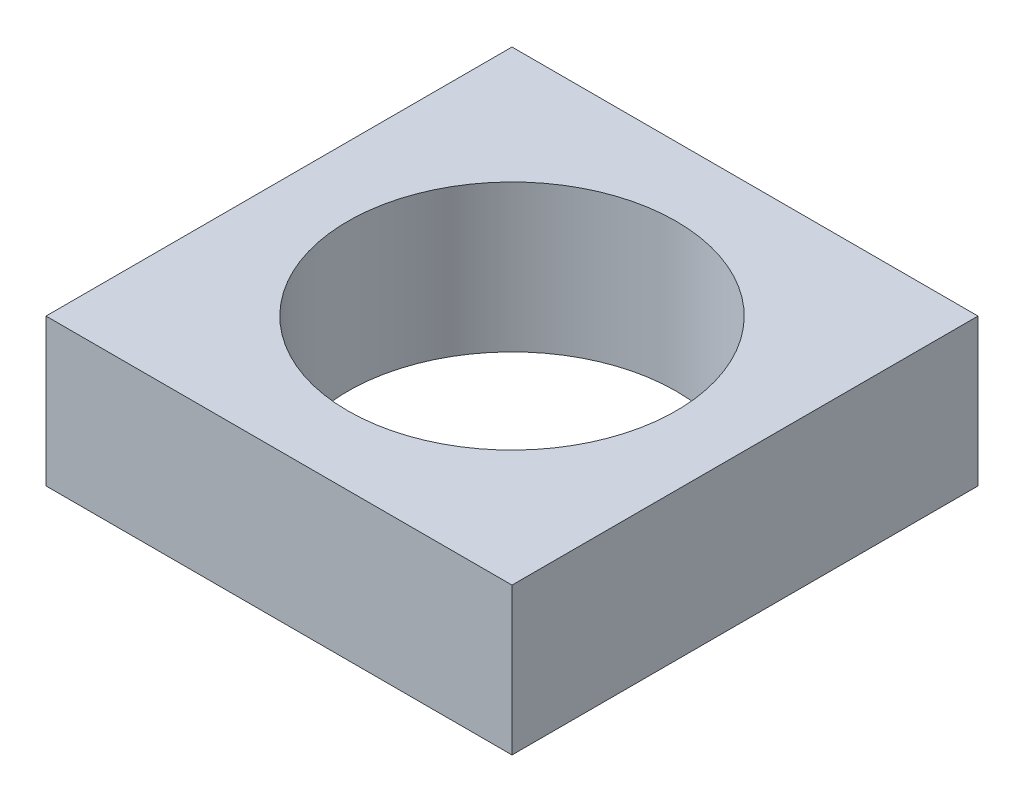
SolidWorks part; units mm, degrees
ref_plane "Front Plane" through (0, 0, 0) normal (0, 0, 1) x (1, 0, 0)
ref_plane "Top Plane" through (0, 0, 0) normal (0, 1, 0) x (1, 0, 0)
ref_plane "Right Plane" through (0, 0, 0) normal (1, 0, 0) x (0, 0, -1)
sketch "Sketch1" plane through (0, 0, 0) normal (0, 1, 0) x (1, 0, 0)
  line L1 (-4.826, -4.826) -> (4.826, -4.826)
  line L2 (-4.826, -4.826) -> (-4.826, 4.826)
  line L3 (-4.826, 4.826) -> (4.826, 4.826)
  line L4 (4.826, -4.826) -> (4.826, 4.826)
  line L5 (-4.826, -4.826) -> (4.826, 4.826) construction
  line L6 (-4.826, 4.826) -> (4.826, -4.826) construction
  circle A0 centre (0, 0) radius 3.4011
  point P0 (0, 0)
  dimension "D2" = 6.8021
  dimension "D1" = 9.652
extrude "Boss-Extrude1" add sketch "Sketch1" along normal blind 3.048
